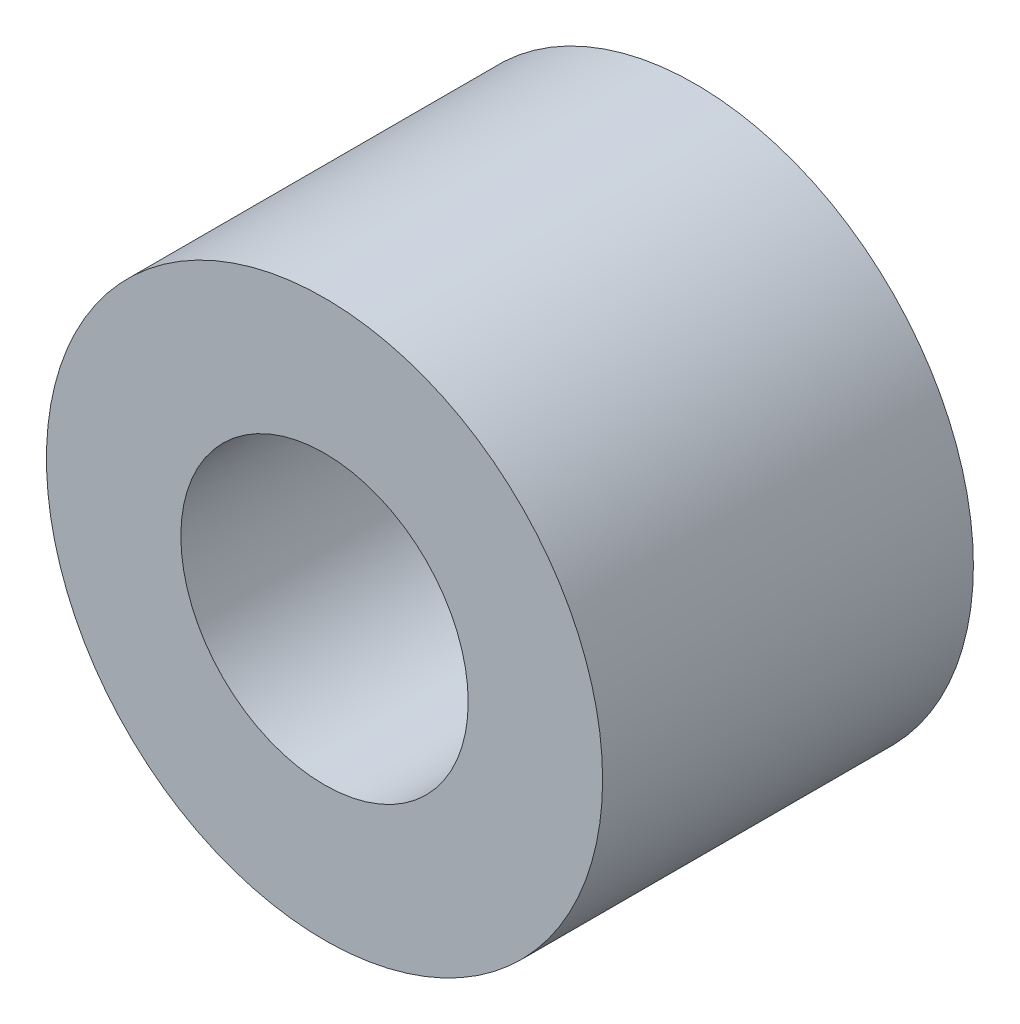
SolidWorks part; units mm, degrees
ref_plane "Plan de face" through (0, 0, 0) normal (0, 0, 1) x (1, 0, 0)
ref_plane "Plan de dessus" through (0, 0, 0) normal (0, 1, 0) x (1, 0, 0)
ref_plane "Plan de droite" through (0, 0, 0) normal (1, 0, 0) x (0, 0, -1)
sketch "Esquisse1" plane through (0, 0, 0) normal (0, 0, 1) x (1, 0, 0)
  circle A0 centre (0, 0) radius 3
  circle A1 centre (0, 0) radius 1.55
extrude "Extrusion1" add sketch "Esquisse1" along normal blind 4
